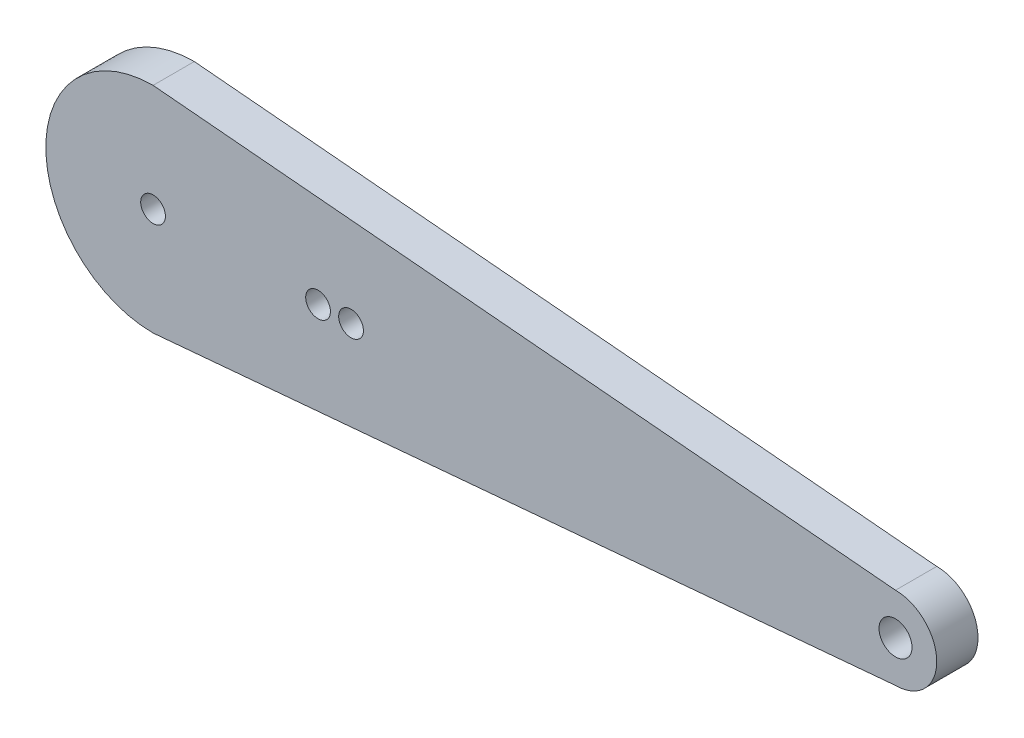
SolidWorks part; units mm, degrees
material "Thornel Mat VMA"
ref_plane "前视基准面" through (0, 0, 0) normal (0, 0, 1) x (1, 0, 0)
ref_plane "上视基准面" through (0, 0, 0) normal (0, 1, 0) x (1, 0, 0)
ref_plane "右视基准面" through (0, 0, 0) normal (1, 0, 0) x (0, 0, -1)
sketch "草图1" plane through (0, 0, 0) normal (0, 0, 1) x (1, 0, 0)
  line L0 (-45, 13) -> (45, 5)
  line L1 (-45, -13) -> (45, -5)
  line L2 (0, -2.75) -> (0, 2.75) construction
  circle A0 centre (-45, 0) radius 1.5
  arc A1 (-45, 13) -> (-45, -13) centre (-45, 0) ccw
  arc A2 (45, 5) -> (45, -5) centre (45, 0) cw
  circle A3 centre (45, 0) radius 2
  circle A4 centre (-25, 0) radius 1.5
  circle A5 centre (-21, 0) radius 1.5
  dimension "D2" = 3
  dimension "D3" = 26
  dimension "D4" = 5
  dimension "D5" = 4
  dimension "D6" = 3
  dimension "D7" = 3
  dimension "D1" = 45
  dimension "D8" = 20
  dimension "D9" = 4
extrude "凸台-拉伸1" add sketch "草图1" along normal blind 5
